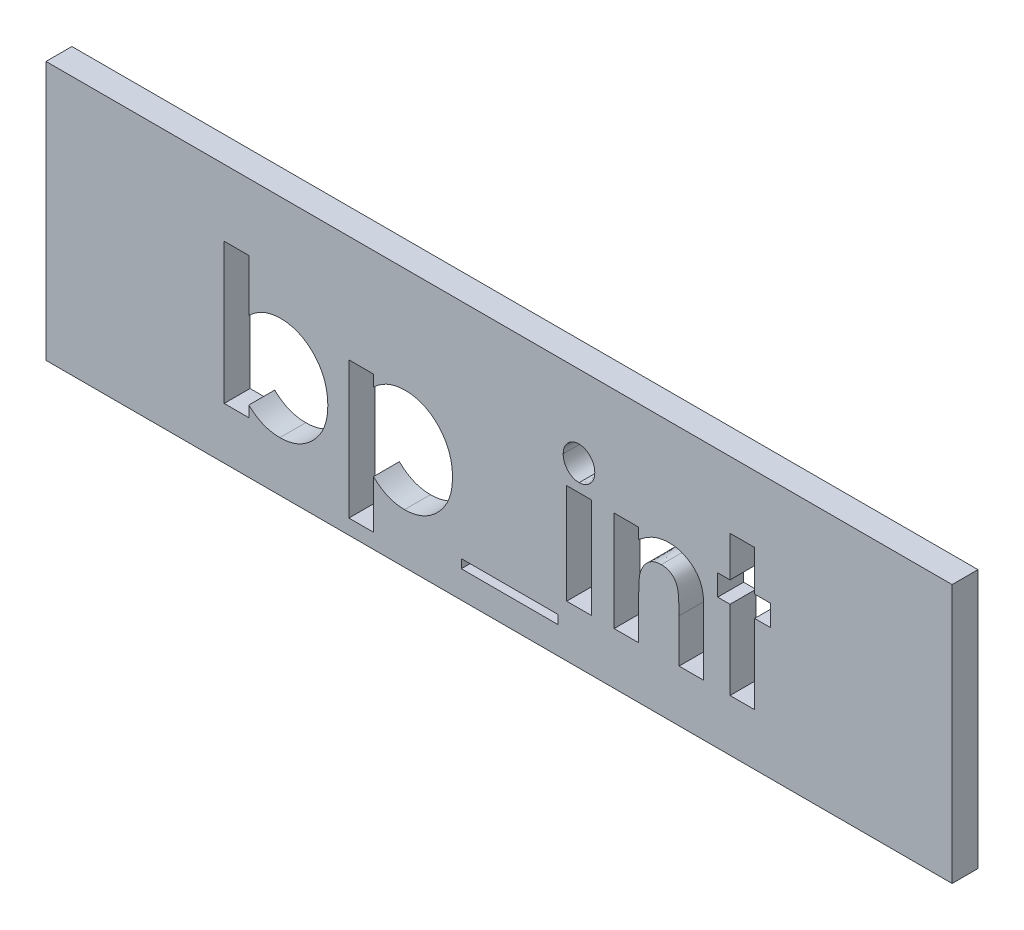
SolidWorks part; units mm, degrees
ref_plane "Plan de face" through (0, 0, 0) normal (0, 0, 1) x (1, 0, 0)
ref_plane "Plan de dessus" through (0, 0, 0) normal (0, 1, 0) x (1, 0, 0)
ref_plane "Plan de droite" through (0, 0, 0) normal (1, 0, 0) x (0, 0, -1)
sketch "Esquisse1" plane through (0, 0, 0) normal (0, 0, 1) x (1, 0, 0)
  line L1 (0, 0) -> (35, 0)
  line L2 (0, 0) -> (0, -10)
  line L3 (0, -10) -> (35, -10)
  line L4 (35, 0) -> (35, -10)
  dimension "D1" = 35
  dimension "D2" = 10
extrude "Boss.-Extru.1" add sketch "Esquisse1" along normal blind 1
sketch "Esquisse2" plane through (0, 0, 0) normal (0, 0, -1) x (-1, 0, 0)
  line L0 (-35, 0) -> (0, 0) construction
  line L1 (-35, -10) -> (-35, 0) construction
  line L2 (0, 0) -> (0, -10) construction
  circle A0 centre (-30, -5) radius 1
  circle A1 centre (-5, -5) radius 1
  dimension "D4" = 2
  dimension "D1" = 5
  dimension "D2" = 5
  dimension "D3" = 5
extrude "Boss.-Extru.2" add sketch "Esquisse2" along normal blind 3
chamfer "Chanfrein1" distance 0.5 angle 45 2 edges at (29, -5, -3) (4, -5, -3)
sketch "Esquisse3" plane through (0, 0, 1) normal (0, 0, 1) x (1, 0, 0)
  line L0 (5, -8) -> (30, -8) construction
  line L3 (0, -10) -> (35, -10) construction
  line L4 (0, 0) -> (0, -10) construction
  line L5 (35, -10) -> (35, 0) construction
  text T1 "<b>bp_int</b>" font "Century Gothic" height in points 20
  point P12 (30, -8)
  dimension "D1" = 2
  dimension "D2" = 5
  dimension "D3" = 25
  dimension "D4" = 5
extrude "Enlèv. mat.-Extru.2" cut sketch "Esquisse3" against normal blind 1
